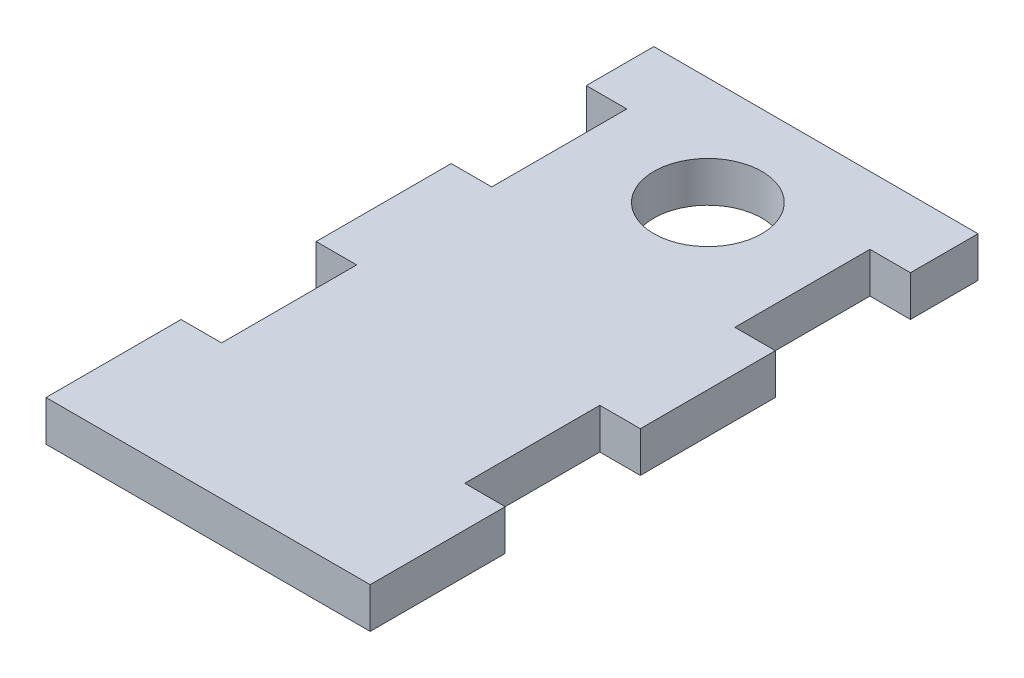
SolidWorks part; units mm, degrees
material "PC High Viscosity"
ref_plane "Front Plane" through (0, 0, 0) normal (0, 0, 1) x (1, 0, 0)
ref_plane "Top Plane" through (0, 0, 0) normal (0, 1, 0) x (1, 0, 0)
ref_plane "Right Plane" through (0, 0, 0) normal (1, 0, 0) x (0, 0, -1)
sketch "Sketch1" plane through (0, 0, 0) normal (0, 1, 0) x (1, 0, 0)
  line L1 (12, -22.5) -> (-12, -22.5)
  line L2 (12, -22.5) -> (12, 22.5)
  line L3 (12, 22.5) -> (-12, 22.5)
  line L4 (-12, -22.5) -> (-12, 22.5)
  line L5 (12, -22.5) -> (-12, 22.5) construction
  line L6 (12, 22.5) -> (-12, -22.5) construction
  point P0 (0, 0)
  dimension "D1" = 24
  dimension "D2" = 45
extrude "Boss-Extrude1" add sketch "Sketch1" along normal blind 3
sketch "Sketch4" plane through (0, 3, 0) normal (0, 1, 0) x (1, 0, 0)
  line L1 (-12, -22.5) -> (12, -22.5) construction
  line L2 (-12, 22.5) -> (-12, -22.5) construction
  line L3 (-12, -12.5) -> (-9, -12.5)
  line L7 (-12, -12.5) -> (-12, -2.5)
  line L8 (-12, -2.5) -> (-9, -2.5)
  line L9 (-9, -12.5) -> (-9, -2.5)
  line L10 (-12, -2.5) -> (-12, 7.5) construction
  line L11 (-12, 7.5) -> (-9, 7.5)
  line L12 (-12, 7.5) -> (-12, 17.5)
  line L13 (-12, 17.5) -> (-9, 17.5)
  line L14 (-9, 7.5) -> (-9, 17.5)
  line L15 (-12, -22.5) -> (-12, -12.5) construction
  line L16 (0, -22.5) -> (0, 22.5) construction
  line L17 (12, 22.5) -> (-12, 22.5) construction
  line L18 (9, 7.5) -> (9, 17.5)
  line L19 (12, 17.5) -> (9, 17.5)
  line L20 (12, 7.5) -> (12, 17.5)
  line L21 (12, 7.5) -> (9, 7.5)
  line L22 (9, -12.5) -> (9, -2.5)
  line L23 (12, -2.5) -> (9, -2.5)
  line L25 (12, -12.5) -> (12, -2.5)
  line L26 (12, -12.5) -> (9, -12.5)
  circle A0 centre (0, 14.5) radius 4
  dimension "D2" = 8
  dimension "D1" = 37
  dimension "D3" = 10
  dimension "D4" = 3
extrude "Cut-Extrude1" cut sketch "Sketch4" against normal through all
equation "\"pulley_pitch_diam\"= 12.73mm"
equation "\"pulley_total_width\"= 16mm"
equation "\"pulley_total_diam\"= 16mm"
equation "\"belt_width\"= 6mm"
equation "\"material_thickness\"= 3mm"
equation "\"shaft_diam\"= 8mm"
equation "\"bearing_od\"= 22mm"
equation "\"bearing_thickness\"= 7mm"
equation "\"D4@Sketch4\"=\"material_thickness\""
